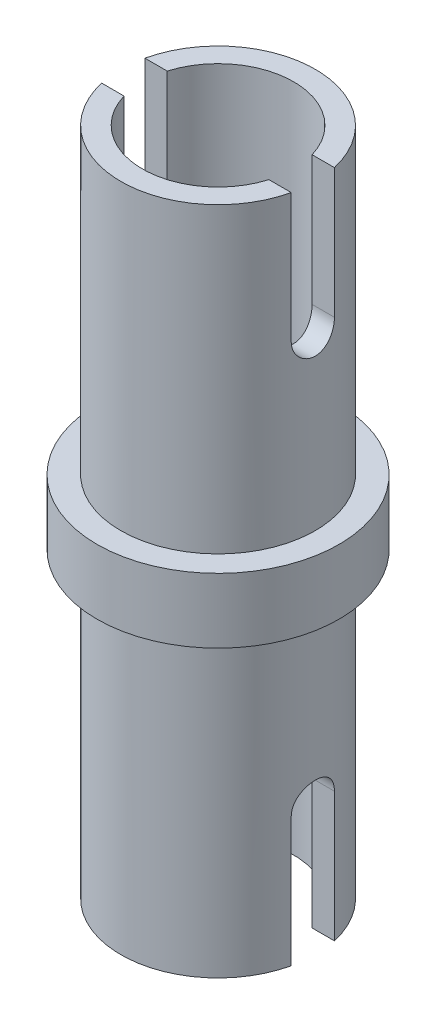
SolidWorks part; units mm, degrees
ref_plane "Front Plane" through (0, 0, 0) normal (0, 0, 1) x (1, 0, 0)
ref_plane "Top Plane" through (0, 0, 0) normal (0, 1, 0) x (1, 0, 0)
ref_plane "Right Plane" through (0, 0, 0) normal (1, 0, 0) x (0, 0, -1)
sketch "Sketch1" plane through (0, 0, 0) normal (0, 1, 0) x (1, 0, 0)
  circle A0 centre (0, 0) radius 2.8
  dimension "D1" = 5.6
extrude "Boss-Extrude1" add sketch "Sketch1" along normal blind 1.5
sketch "Sketch2" plane through (0, 1.5, 0) normal (0, 1, 0) x (1, 0, 0)
  circle A0 centre (0, 0) radius 2.25
  dimension "D1" = 4.5
extrude "Boss-Extrude2" add sketch "Sketch2" along normal blind 7
sketch "Sketch3" plane through (0, 0, 0) normal (0, -1, 0) x (1, 0, 0)
  circle A0 centre (0, 0) radius 2.25
  dimension "D1" = 4.5
extrude "Boss-Extrude3" add sketch "Sketch3" along normal blind 7
ref_plane "Plane1" through (100, 0, 0) normal (1, 0, 0) x (0, 0, -1)
sketch "Sketch4" plane through (100, 0, 0) normal (1, 0, 0) x (0, 0, -1)
  line L0 (0, 1.5) -> (0, 5.5) construction
  line L1 (2.8, 1.5) -> (-2.8, 1.5) construction
  line L2 (0, 0) -> (0, -4) construction
  line L3 (0, 5.5) -> (0, 8.5) construction
  line L4 (2.25, 8.5) -> (-2.25, 8.5) construction
  line L5 (-0.5, 5.5) -> (-0.5, 8.5)
  line L6 (0.5, 5.5) -> (0.5, 8.5)
  line L7 (0, -4) -> (0, -7) construction
  line L8 (-2.25, -7) -> (2.25, -7) construction
  line L9 (0.5, -4) -> (0.5, -7)
  line L10 (-0.5, -4) -> (-0.5, -7)
  arc A0 (-0.5, 5.5) -> (0.5, 5.5) centre (0, 5.5) ccw
  arc A1 (0.5, 8.5) -> (-0.5, 8.5) centre (0, 8.5) ccw
  arc A2 (0.5, -4) -> (-0.5, -4) centre (0, -4) ccw
  arc A3 (-0.5, -7) -> (0.5, -7) centre (0, -7) ccw
  point P7 (0, 7)
  point P15 (0, -5.5)
  dimension "D1" = 4
  dimension "D2" = 4
extrude "Cut-Extrude1" cut sketch "Sketch4" against normal through all
ref_plane "Plane2" through (0, 100, 0) normal (0, 1, 0) x (1, 0, 0)
sketch "Sketch5" plane through (0, 100, 0) normal (0, 1, 0) x (1, 0, 0)
  circle A0 centre (0, 0) radius 1.75
  dimension "D1" = 3.5
extrude "Cut-Extrude2" cut sketch "Sketch5" against normal through all
